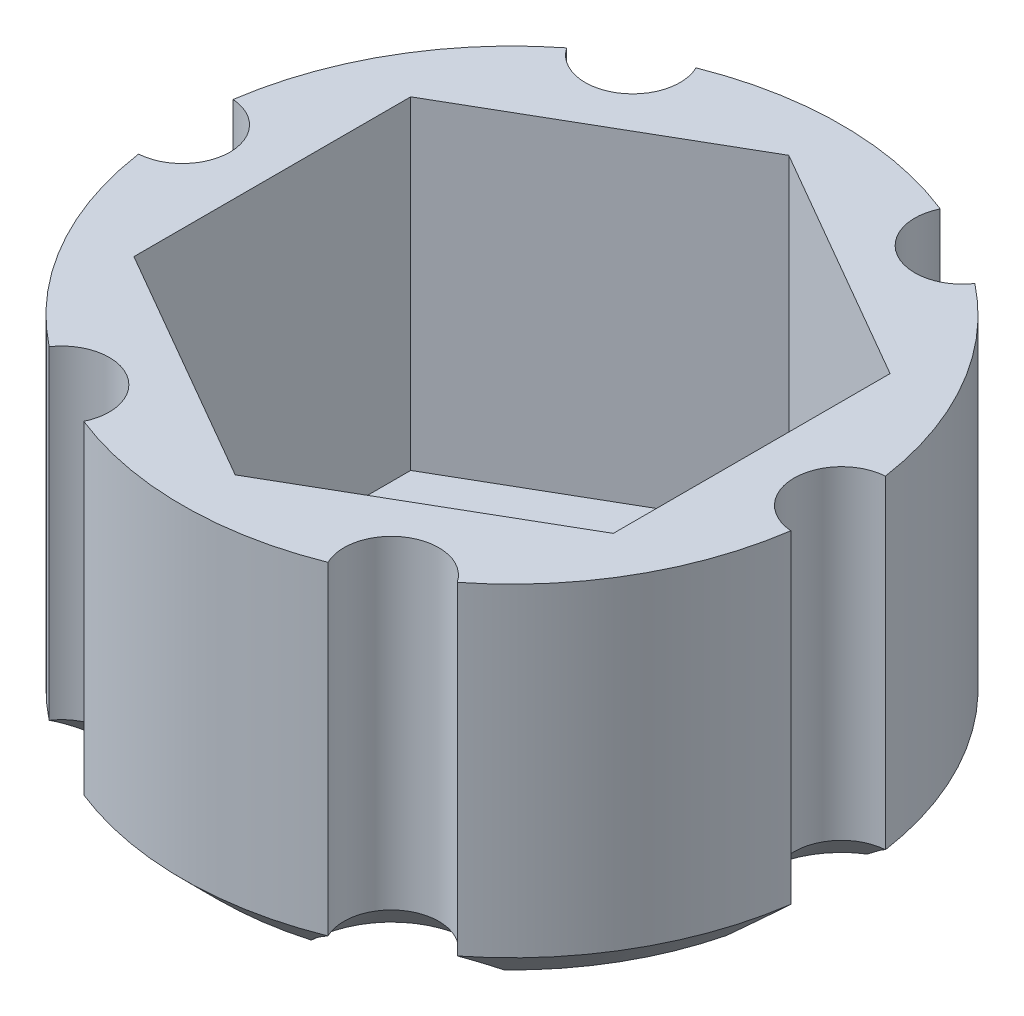
SolidWorks part; units mm, degrees
ref_plane "Front Plane" through (0, 0, 0) normal (0, 0, 1) x (1, 0, 0)
ref_plane "Top Plane" through (0, 0, 0) normal (0, 1, 0) x (1, 0, 0)
ref_plane "Right Plane" through (0, 0, 0) normal (1, 0, 0) x (0, 0, -1)
sketch "Sketch1" plane through (0, 0, 0) normal (0, 1, 0) x (1, 0, 0)
  circle A1 centre (0, 0) radius 5.5
  dimension "D2" = 11
sketch "Sketch2" plane through (0, 0, 0) normal (0, 1, 0) x (1, 0, 0)
  line L1 (4, -2.3094) -> (4, 2.3094)
  line L2 (4, 2.3094) -> (0, 4.6188)
  line L3 (0, 4.6188) -> (-4, 2.3094)
  line L4 (-4, 2.3094) -> (-4, -2.3094)
  line L5 (-4, -2.3094) -> (0, -4.6188)
  line L6 (0, -4.6188) -> (4, -2.3094)
  circle A0 centre (0, 0) radius 4 construction
  dimension "D1" = 8
extrude "Boss-Extrude1" add sketch "Sketch1" along normal blind 6
extrude "Cut-Extrude1" cut sketch "Sketch2" against normal blind 5.4 from surface at 6 contours L6 L1 L2 L3 L4 L5 starting at face at (0, 6, 5.5)
sketch "Sketch3" plane through (0, 0, 0) normal (0, 1, 0) x (1, 0, 0)
  circle A0 centre (-5.5, 0) radius 0.7918
  circle A1 centre (0, 0) radius 5.5 construction
  circle A2 centre (-2.75, 4.7631) radius 0.7918
  circle A3 centre (2.75, 4.7631) radius 0.7918
  circle A4 centre (5.5, 0) radius 0.7918
  circle A5 centre (2.75, -4.7631) radius 0.7918
  circle A6 centre (-2.75, -4.7631) radius 0.7918
  dimension "D1" = 6
extrude "Cut-Extrude2" cut sketch "Sketch3" along normal up to surface (6 mm away) from surface at 0 up to face at (0, 6, 5.5) starting at face at (0, 0, 5.5)
chamfer "Chamfer1" distance 0.6 angle 45 12 edges at (-4.7631, 0, 2.75) (-2.3541, 0, 4.0774) (0, 0, 5.5) (2.3541, 0, 4.0774) (4.7631, 0, 2.75) (4.7082, 0, 0) (4.7631, 0, -2.75) (2.3541, 0, -4.0774) (0, 0, -5.5) (-2.3541, 0, -4.0774) (-4.7631, 0, -2.75) (-4.7082, 0, 0)
